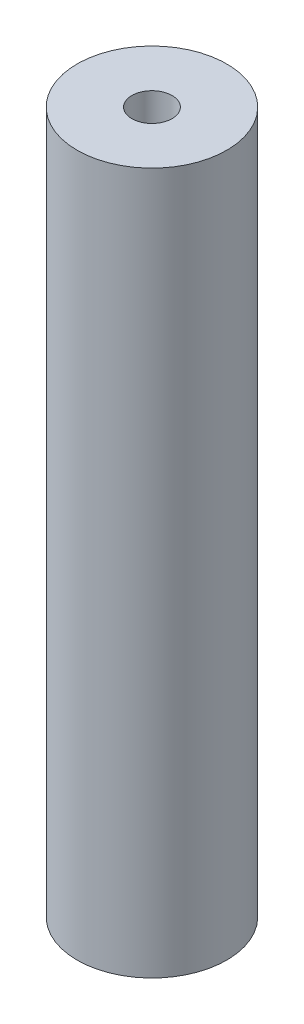
SolidWorks part; units mm, degrees
ref_plane "Alzado" through (0, 0, 0) normal (0, 0, 1) x (1, 0, 0)
ref_plane "Planta" through (0, 0, 0) normal (0, 1, 0) x (1, 0, 0)
ref_plane "Vista lateral" through (0, 0, 0) normal (1, 0, 0) x (0, 0, -1)
sketch "Croquis1" plane through (0, 0, 0) normal (0, 1, 0) x (1, 0, 0)
  circle A0 centre (0, 0) radius 16
  circle A1 centre (0, 0) radius 4.3
  dimension "D1" = 8.6
  dimension "D2" = 32
extrude "Saliente-Extruir1" add sketch "Croquis1" along normal blind 150
